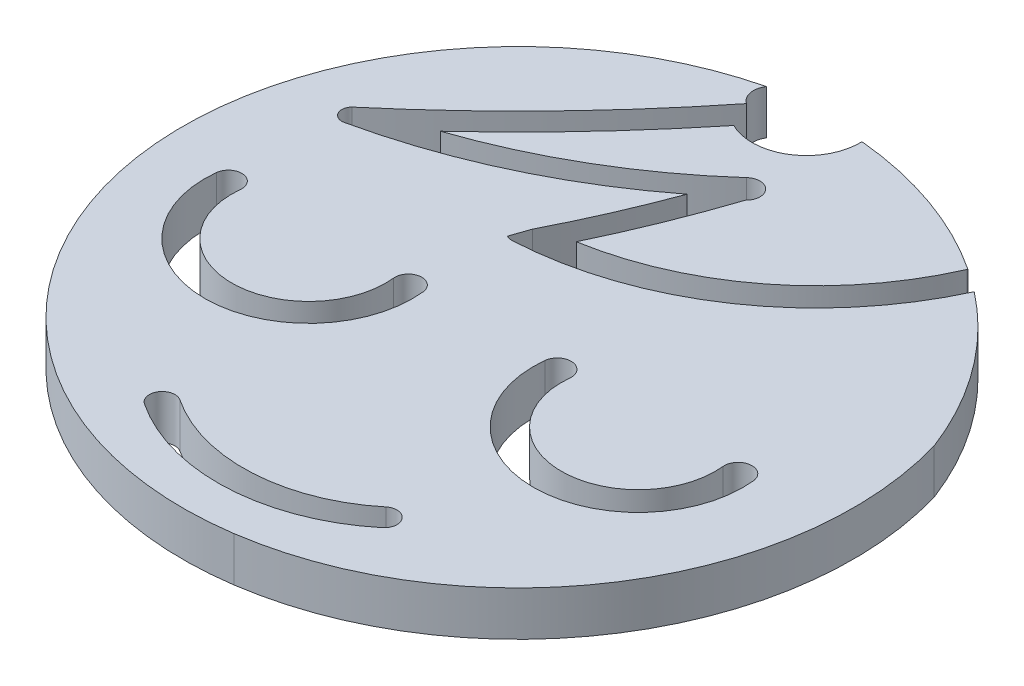
SolidWorks part; units mm, degrees
ref_plane "Alzado" through (0, 0, 0) normal (0, 0, 1) x (1, 0, 0)
ref_plane "Planta" through (0, 0, 0) normal (0, 1, 0) x (1, 0, 0)
ref_plane "Vista lateral" through (0, 0, 0) normal (1, 0, 0) x (0, 0, -1)
sketch "Croquis1" plane through (0, 0, 0) normal (0, 1, 0) x (1, 0, 0)
  line L0 (0, 0) -> (0, 60) construction
  line L1 (45.4256, 39.2063) -> (44.9931, 37.9533)
  arc A0 (45.3133, 53.752) -> (44.9931, 55.4203) centre (45.9873, 54.7462) cw
  arc A1 (44.9931, 55.4203) -> (28.666, 40.1086) centre (50.4163, 33.2767) ccw
  arc A2 (47.6409, 39.9502) -> (62.4243, 51.4925) centre (44.2991, 59.4687) ccw
  arc A3 (31.4718, 31.8621) -> (45.4048, 31.8621) centre (38.4383, 31.1201) ccw
  arc A4 (33.2714, 31.6704) -> (43.6051, 31.6704) centre (38.4383, 31.1201) ccw
  arc A5 (33.2714, 31.6704) -> (31.4718, 31.8621) centre (32.3716, 31.7663) ccw
  arc A6 (45.4048, 31.8621) -> (43.6051, 31.6704) centre (44.5049, 31.7663) ccw
  arc A7 (47.6409, 39.9502) -> (50.9184, 48.0743) centre (-14.6018, 69.7838) ccw
  arc A8 (53.5136, 31.9586) -> (67.571, 31.9586) centre (60.5423, 31.2324) ccw
  arc A9 (55.3815, 31.7656) -> (65.7031, 31.7656) centre (60.5423, 31.2324) ccw
  arc A10 (55.3815, 31.7656) -> (53.5136, 31.9586) centre (54.4475, 31.8621) ccw
  arc A11 (67.571, 31.9586) -> (65.7031, 31.7656) centre (66.637, 31.8621) ccw
  arc A12 (28.666, 40.1086) -> (53.1364, 11.3737) centre (49.9296, 33.4296) ccw
  arc A13 (53.1364, 11.3737) -> (71.6135, 40.1086) centre (49.8792, 33.7761) ccw
  arc A14 (71.6135, 40.1086) -> (63.9708, 50.4461) centre (49.2158, 31.5435) ccw
  arc A15 (46.1636, 52.0434) -> (51.4336, 55.4203) centre (47.7848, 55.314) ccw
  arc A16 (49.6429, 49.4386) -> (50.9184, 48.0743) centre (50.2806, 48.7564) cw
  arc A17 (62.4477, 51.5418) -> (51.4336, 55.4203) centre (49.2158, 31.5435) ccw
  arc A21 (42.5564, 15.924) -> (57.8014, 16.7238) centre (49.6397, 26.6026) ccw
  arc A22 (43.5088, 17.3597) -> (56.7041, 18.0519) centre (49.6397, 26.6026) ccw
  arc A23 (43.5088, 17.3597) -> (42.5564, 15.924) centre (43.0326, 16.6419) ccw
  arc A24 (57.8014, 16.7238) -> (56.7041, 18.0519) centre (57.2527, 17.3879) ccw
  arc A36 (45.4539, 37.8574) -> (63.9708, 50.4461) centre (44.2991, 59.4687) ccw
  arc A38 (44.9931, 37.9533) -> (45.4539, 37.8574) centre (45.4048, 38.7759) ccw
  arc A39 (62.4477, 51.5418) -> (62.4243, 51.4925) centre (63.2662, 51.122) ccw
  arc A41 (36.6046, 41.8185) -> (49.6429, 49.4386) centre (24.4461, 77.5866) ccw
  arc A42 (32.2272, 40.2595) -> (45.3133, 53.752) centre (-28.8919, 112.6301) ccw
  arc A43 (32.2272, 40.2595) -> (32.8788, 39.1004) centre (32.7056, 39.7658) ccw
  arc A46 (32.8788, 39.1004) -> (48.5977, 46.4579) centre (24.4461, 77.5866) ccw
  arc A52 (45.4256, 39.2063) -> (48.5977, 46.4579) centre (-14.6018, 69.7838) ccw
  arc A54 (36.6046, 41.8185) -> (46.1636, 52.0434) centre (-28.8919, 112.6301) ccw
  point P9 (38.4383, 25.0191)
  point P14 (60.5423, 25.1052)
  point P41 (50.2659, 14.6662)
  point P46 (22.7168, 31.3642)
  point P54 (77.7852, 31.3147)
  point P65 (56.0819, 42.4223)
  point P70 (39.1778, 45.8874)
  point P78 (41.9148, 43.0398)
  point P86 (48.41, 43.7057)
extrude "Saliente-Extruir1" add sketch "Croquis1" along normal blind 3
equation "\"ç\"=0.5"
